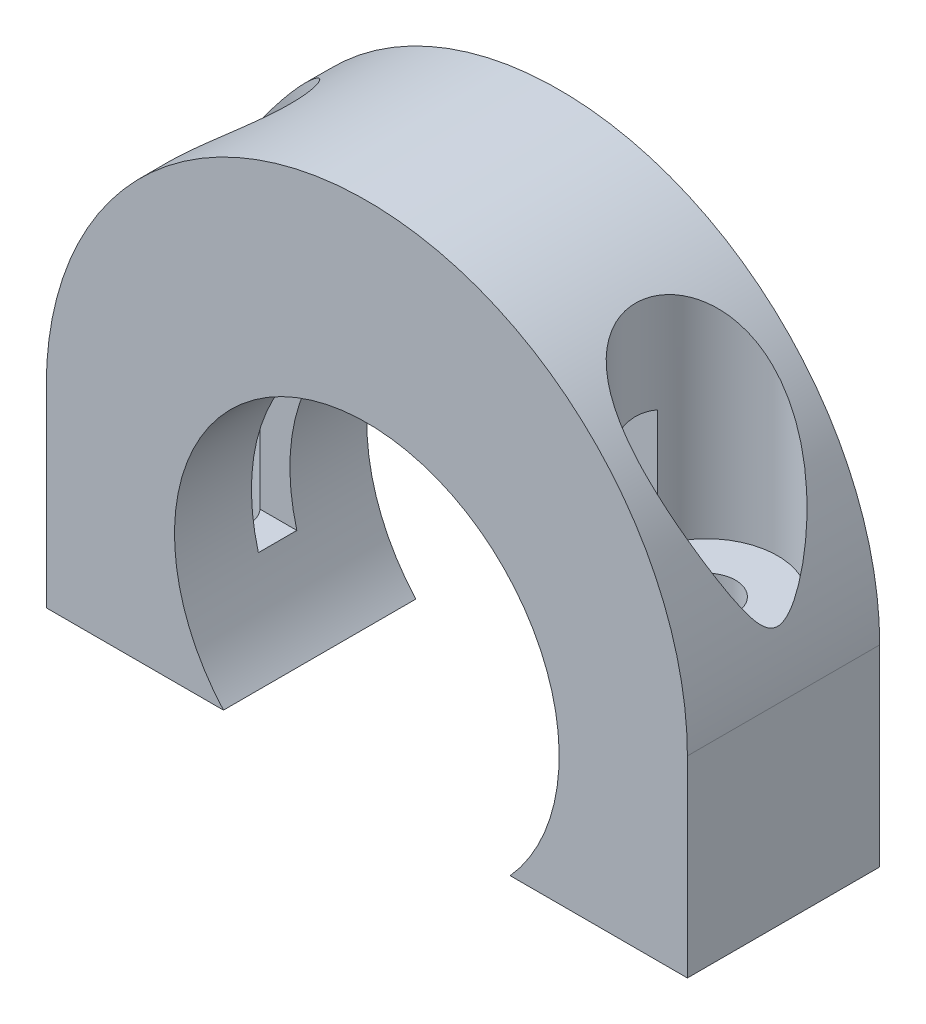
SolidWorks part; units mm, degrees
material "ABS"
ref_plane "Ön Düzlem" through (0, 0, 0) normal (0, 0, 1) x (1, 0, 0)
ref_plane "Üst Düzlem" through (0, 0, 0) normal (0, 1, 0) x (1, 0, 0)
ref_plane "Sağ Düzlem" through (0, 0, 0) normal (1, 0, 0) x (0, 0, -1)
sketch "Sketch1" plane through (0, 0, 0) normal (0, 0, 1) x (1, 0, 0)
  line L0 (-25, 0) -> (-25, -15)
  line L3 (25, 0) -> (25, -15)
  line L4 (25, -15) -> (-25, -15)
  arc A0 (25, 0) -> (-25, 0) centre (0, 0) ccw
  dimension "D1" = 50
  dimension "D2" = 15
extrude "Boss-Extrude1" add sketch "Sketch1" along normal blind 15 contours A0 L0 L4 L3
shell "Shell2" thickness 6
sketch "Sketch2" plane through (0, 0, 15) normal (0, 0, 1) x (1, 0, 0)
  line L0 (0, 0) -> (0, -28.057) construction
  circle A1 centre (0, -5) radius 15
  dimension "D1" = 30
  dimension "D2" = 5
extrude "Cut-Extrude1" cut sketch "Sketch2" against normal up to next
ref_plane "Plane1" through (0, 25, 0) normal (0, 1, 0) x (1, 0, 0)
sketch "Sketch3" plane through (0, 25, 0) normal (0, 1, 0) x (1, 0, 0)
  line L0 (0, -15) -> (0, 6.4883) construction
  line L1 (-25, -15) -> (25, -15) construction
  line L2 (25, 0) -> (-25, 0) construction
  line L6 (25, -15) -> (25, 0) construction
  circle A0 centre (-19, -7.5) radius 2.25
  circle A1 centre (19, -7.5) radius 2.25
  point P15 (0, 0)
  dimension "D1" = 6
  dimension "D2" = 7.5
extrude "Cut-Extrude2" cut sketch "Sketch3" against normal up to next
sketch "Sketch5" plane through (0, 25, 0) normal (0, 1, 0) x (1, 0, 0)
  line L1 (0, -15) -> (0, 7.0258) construction
  line L2 (-25, -15) -> (25, -15) construction
  circle A0 centre (19, -7.5) radius 5.54
  circle A1 centre (-19, -7.5) radius 5.54
extrude "Cut-Extrude3" cut sketch "Sketch5" against normal blind 21
